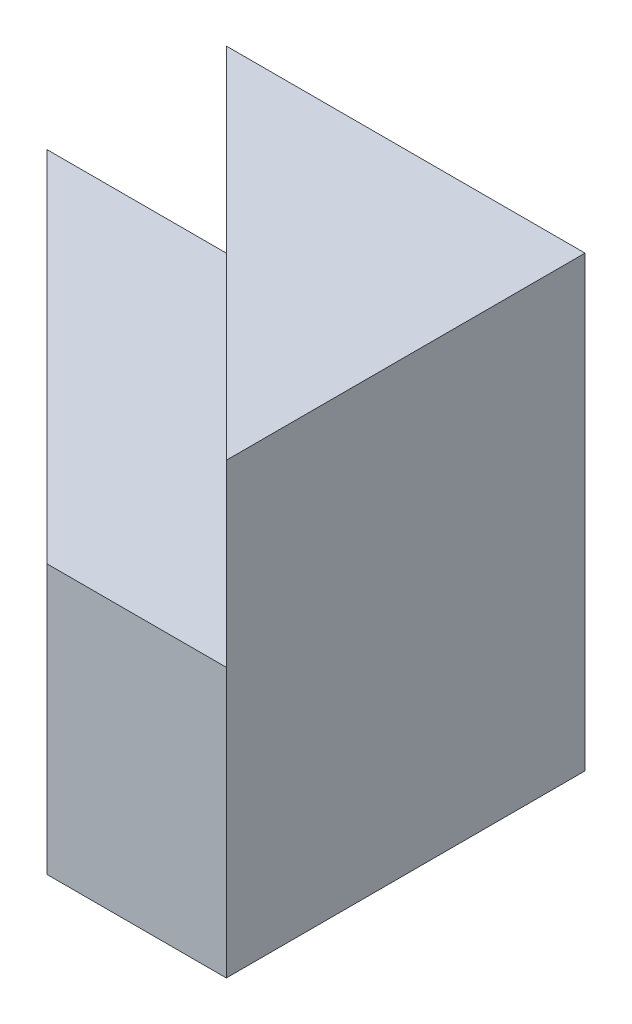
SolidWorks part; units mm, degrees
ref_plane "Front Plane" through (0, 0, 0) normal (0, 0, 1) x (1, 0, 0)
ref_plane "Top Plane" through (0, 0, 0) normal (0, 1, 0) x (1, 0, 0)
ref_plane "Right Plane" through (0, 0, 0) normal (1, 0, 0) x (0, 0, -1)
sketch "Sketch1" plane through (0, 0, 0) normal (0, 1, 0) x (1, 0, 0)
  line L1 (0, 0) -> (6, 0)
  line L2 (0, 0) -> (0, 4)
  line L3 (0, 4) -> (6, 4)
  line L4 (6, 0) -> (6, 4)
  dimension "D1" = 6
  dimension "D2" = 4
extrude "Boss-Extrude1" add sketch "Sketch1" along normal blind 3
sketch "Sketch3" plane through (0, 3, 0) normal (0, 1, 0) x (1, 0, 0)
  line L0 (6, 4) -> (6, 0)
  line L2 (0, 0) -> (6, 0) construction
  line L3 (6, 0) -> (2, 4)
  line L4 (6, 4) -> (0, 4) construction
  line L5 (2, 4) -> (6, 4)
  dimension "D1" = 4
extrude "Boss-Extrude2" add sketch "Sketch3" along normal blind 2
sketch "Sketch4" plane through (0, 3, 0) normal (0, 1, 0) x (1, 0, 0)
  line L0 (4, 0) -> (0, 4)
  line L1 (0, 0) -> (6, 0) construction
  line L2 (0, 4) -> (0, 0)
  line L3 (0, 0) -> (4, 0)
  dimension "D1" = 2
extrude "Cut-Extrude1" cut sketch "Sketch4" against normal blind 10
